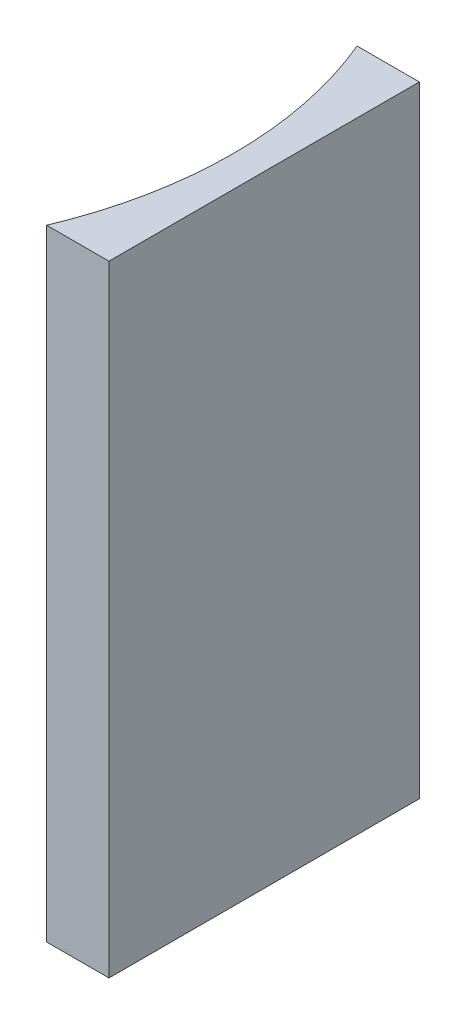
SolidWorks part; units mm, degrees
ref_plane "前视基准面" through (0, 0, 0) normal (0, 0, 1) x (1, 0, 0)
ref_plane "上视基准面" through (0, 0, 0) normal (0, 1, 0) x (1, 0, 0)
ref_plane "右视基准面" through (0, 0, 0) normal (1, 0, 0) x (0, 0, -1)
sketch "草图1" plane through (0, 0, 0) normal (0, 1, 0) x (1, 0, 0)
  line L0 (0, 0) -> (0, -20)
  line L1 (0, 0) -> (-4.0126, 0)
  line L2 (0, -20) -> (-4.0126, -20)
  line L3 (8.2336, -10) -> (-10.4405, -10) construction
  arc A0 (-4.0126, -20) -> (-4.0126, 0) centre (-27.85, -10) ccw
  point P7 (-2, -10)
  point P8 (0, -10)
  dimension "D2" = 25.85
  dimension "D3" = 2
  dimension "D1" = 20
extrude "凸台-拉伸1" add sketch "草图1" along normal blind 40
